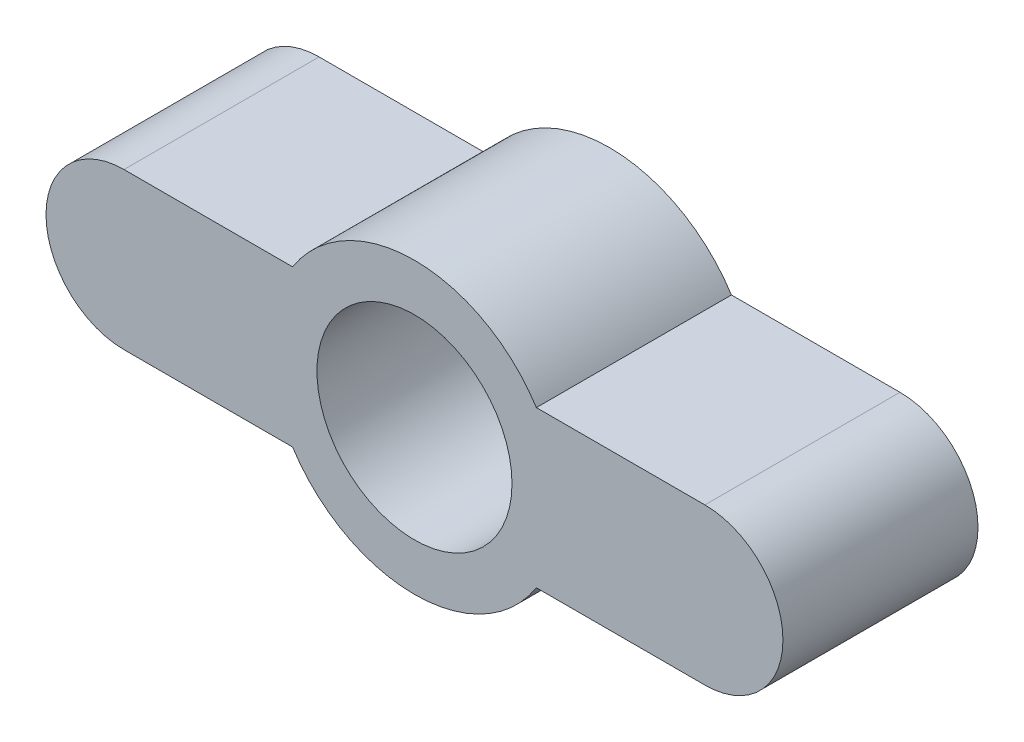
SolidWorks part; units mm, degrees
ref_plane "Front Plane" through (0, 0, 0) normal (0, 0, 1) x (1, 0, 0)
ref_plane "Top Plane" through (0, 0, 0) normal (0, 1, 0) x (1, 0, 0)
ref_plane "Right Plane" through (0, 0, 0) normal (1, 0, 0) x (0, 0, -1)
sketch "Sketch1" plane through (0, 0, 0) normal (0, 0, 1) x (1, 0, 0)
  line L4 (3.1248, -2) -> (7.445, -2)
  line L5 (3.1248, 2) -> (7.445, 2)
  line L6 (-3.1248, -2) -> (-7.445, -2)
  line L7 (-3.1248, 2) -> (-7.445, 2)
  arc A5 (7.445, -2) -> (7.445, 2) centre (7.445, 0) ccw
  arc A6 (-7.445, 2) -> (-7.445, -2) centre (-7.445, 0) ccw
  arc A7 (3.1248, 2) -> (-3.1248, 2) centre (0, 0) ccw
  arc A8 (-3.1248, -2) -> (3.1248, -2) centre (0, 0) ccw
  circle A9 centre (0, 0) radius 2.5
extrude "Boss-Extrude1" add sketch "Sketch1" along normal blind 5
